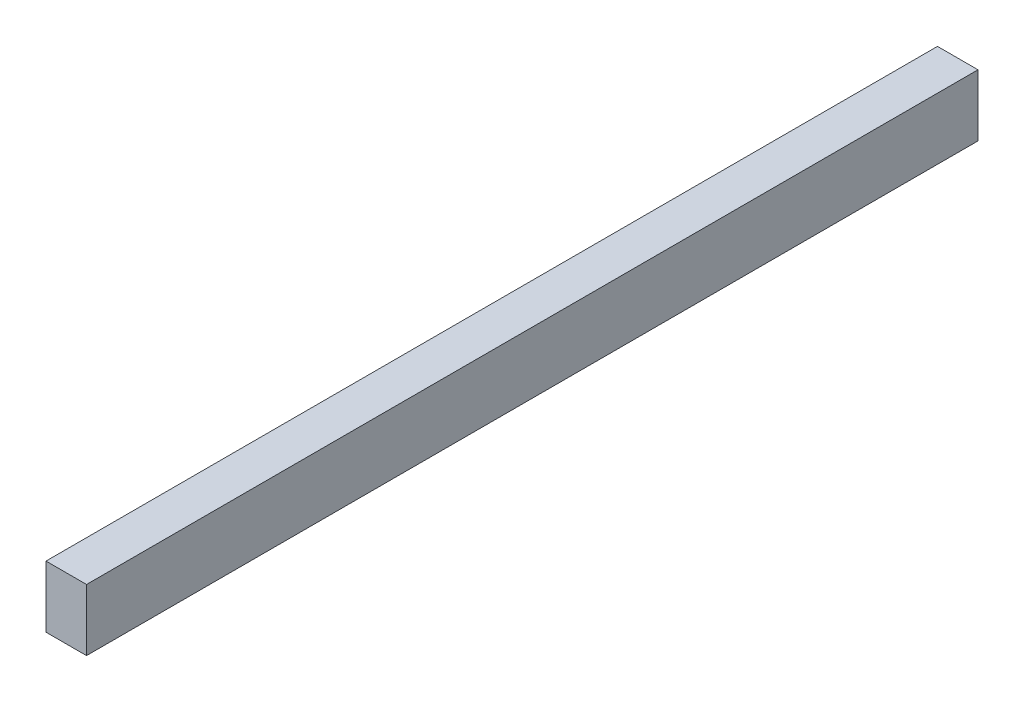
SolidWorks part; units mm, degrees
material "Pine"
ref_plane "Front Plane" through (0, 0, 0) normal (0, 0, 1) x (1, 0, 0)
ref_plane "Top Plane" through (0, 0, 0) normal (0, 1, 0) x (1, 0, 0)
ref_plane "Right Plane" through (0, 0, 0) normal (1, 0, 0) x (0, 0, -1)
sketch "Sketch1" plane through (0, 0, 0) normal (0, 0, 1) x (1, 0, 0)
  line L1 (-24.3148, 49.1477) -> (13.7852, 49.1477)
  line L2 (-24.3148, 49.1477) -> (-24.3148, -8.796)
  line L3 (-24.3148, -8.796) -> (13.7852, -8.796)
  line L4 (13.7852, 49.1477) -> (13.7852, -8.796)
  dimension "D1" = 38.1
  dimension "D2" = 57.9437
extrude "Boss-Extrude1" add sketch "Sketch1" along normal blind 838.2
